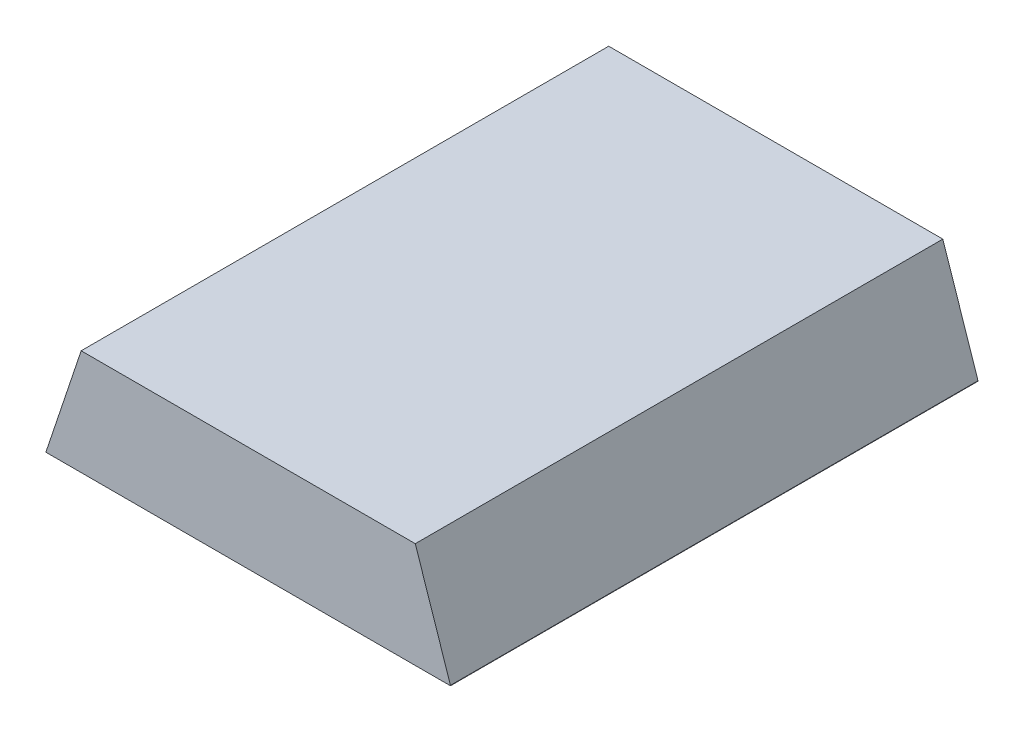
SolidWorks part; units mm, degrees
ref_plane "前视基准面" through (0, 0, 0) normal (0, 0, 1) x (1, 0, 0)
ref_plane "上视基准面" through (0, 0, 0) normal (0, 1, 0) x (1, 0, 0)
ref_plane "右视基准面" through (0, 0, 0) normal (1, 0, 0) x (0, 0, -1)
sketch "草图1" plane through (0, 0, 0) normal (0, 1, 0) x (1, 0, 0)
  line L1 (-0.575, 0.75) -> (0.575, 0.75)
  line L2 (-0.575, 0.75) -> (-0.575, -0.75)
  line L3 (-0.575, -0.75) -> (0.575, -0.75)
  line L4 (0.575, 0.75) -> (0.575, -0.75)
  line L5 (-0.575, 0.75) -> (0.575, -0.75) construction
  line L6 (-0.575, -0.75) -> (0.575, 0.75) construction
  point P0 (0, 0)
  dimension "D1" = 1.15
  dimension "D2" = 1.5
extrude "凸台-拉伸1" add sketch "草图1" along normal blind 0.3
chamfer "倒角1" distance 0.1 angle 71.5 1 edges at (-0.575, 0.3, 0)
chamfer "倒角2" distance 0.1 angle 71.5 1 edges at (0.575, 0.3, 0)
